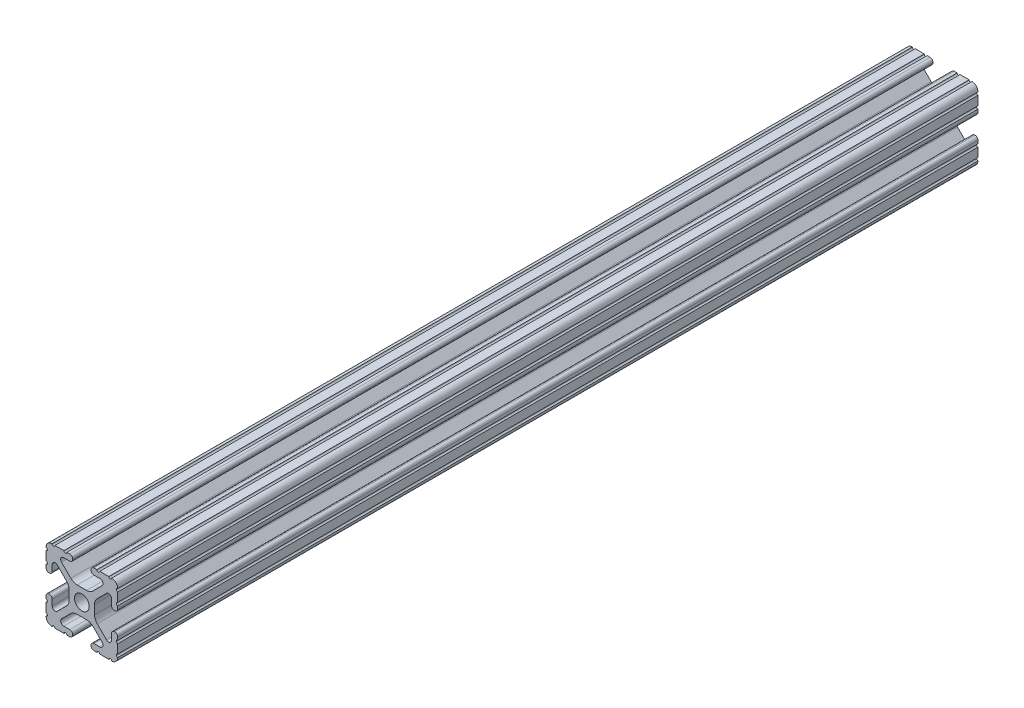
SolidWorks part; units mm, degrees
material "6105-T5 Aluminum"
ref_plane "Front Plane" through (0, 0, 0) normal (0, 0, 1) x (1, 0, 0)
ref_plane "Top Plane" through (0, 0, 0) normal (0, 1, 0) x (1, 0, 0)
ref_plane "Right Plane" through (0, 0, 0) normal (1, 0, 0) x (0, 0, -1)
sketch "Sketch1" plane through (0, 0, 0) normal (0, 0, 1) x (1, 0, 0)
  line L0 (-7.207, 8.7244) -> (-3.8983, 5.4232)
  line L1 (-4.2875, 10.4902) -> (-6.4768, 10.4902)
  line L2 (-3.2385, 11.651) -> (-3.2385, 11.5392)
  line L3 (-5.3171, 12.7) -> (-4.2875, 12.7)
  line L4 (0, 13.4005) -> (0, -14.8534) construction
  line L5 (12.7, 0) -> (-13.9989, 0) construction
  line L6 (-9.5504, 12.7) -> (-6.3331, 12.7)
  line L7 (-12.7, 6.3331) -> (-12.7, 9.5504)
  line L8 (-12.7, 4.2875) -> (-12.7, 5.3171)
  line L9 (-11.5392, 3.2385) -> (-11.651, 3.2385)
  line L10 (-10.4902, 6.4021) -> (-10.4902, 4.2875)
  line L11 (-5.441, 3.8408) -> (-8.7371, 7.1294)
  line L12 (-4.5085, -1.5932) -> (-4.5085, 1.5932)
  line L13 (-1.7093, -4.4958) -> (1.7093, -4.4958)
  line L14 (3.9523, -5.4237) -> (7.1797, -8.6452)
  line L15 (6.4164, -10.4902) -> (4.2875, -10.4902)
  line L16 (3.2385, -11.5392) -> (3.2385, -11.651)
  line L17 (4.2875, -12.7) -> (5.3171, -12.7)
  line L18 (6.3331, -12.7) -> (9.5504, -12.7)
  line L19 (12.7, -9.5504) -> (12.7, -6.3331)
  line L20 (12.7, -5.3171) -> (12.7, -4.2875)
  line L21 (11.651, -3.2385) -> (11.5392, -3.2385)
  line L22 (10.4902, -4.2875) -> (10.4902, -6.4021)
  line L23 (8.7371, -7.1294) -> (5.441, -3.8408)
  line L24 (4.5085, -1.5932) -> (4.5085, 1.5932)
  line L25 (5.441, 3.8408) -> (8.7371, 7.1294)
  line L26 (10.4902, 6.4021) -> (10.4902, 4.2875)
  line L27 (11.5392, 3.2385) -> (11.651, 3.2385)
  line L28 (12.7, 4.2875) -> (12.7, 5.3171)
  line L29 (12.7, 6.3331) -> (12.7, 9.5504)
  line L30 (9.5504, 12.7) -> (6.3331, 12.7)
  line L31 (5.3171, 12.7) -> (4.2875, 12.7)
  line L32 (3.2385, 11.651) -> (3.2385, 11.5392)
  line L33 (4.2875, 10.4902) -> (6.4768, 10.4902)
  line L34 (7.207, 8.7244) -> (3.8983, 5.4232)
  line L35 (1.6558, 4.4958) -> (-1.6558, 4.4958)
  line L36 (-8.7371, -7.1294) -> (-5.441, -3.8408)
  line L37 (-10.4902, -4.2875) -> (-10.4902, -6.4021)
  line L38 (-11.651, -3.2385) -> (-11.5392, -3.2385)
  line L39 (-12.7, -5.3171) -> (-12.7, -4.2875)
  line L40 (-12.7, -9.5504) -> (-12.7, -6.3331)
  line L41 (-6.3331, -12.7) -> (-9.5504, -12.7)
  line L42 (-4.2875, -12.7) -> (-5.3171, -12.7)
  line L43 (-3.2385, -11.5392) -> (-3.2385, -11.651)
  line L44 (-6.4164, -10.4902) -> (-4.2875, -10.4902)
  line L45 (-3.9523, -5.4237) -> (-7.1797, -8.6452)
  arc A0 (-7.207, 8.7244) -> (-6.4768, 10.4902) centre (-6.4768, 9.4563) cw
  arc A1 (-3.2385, 11.5392) -> (-4.2875, 10.4902) centre (-4.2875, 11.5392) cw
  arc A2 (-4.2875, 12.7) -> (-3.2385, 11.651) centre (-4.2875, 11.651) cw
  arc A3 (-5.3171, 12.7) -> (-6.3331, 12.7) centre (-5.8251, 12.7) cw
  arc A4 (-9.5504, 12.7) -> (-10.5664, 12.6998) centre (-10.0584, 12.7) cw
  arc A5 (-12.6998, 10.5664) -> (-10.5664, 12.6998) centre (-10.5918, 10.5918) cw
  arc A6 (-12.6998, 10.5664) -> (-12.7, 9.5504) centre (-12.7, 10.0584) cw
  arc A7 (-12.7, 6.3331) -> (-12.7, 5.3171) centre (-12.7, 5.8251) cw
  arc A8 (-11.651, 3.2385) -> (-12.7, 4.2875) centre (-11.651, 4.2875) cw
  arc A9 (-10.4902, 4.2875) -> (-11.5392, 3.2385) centre (-11.5392, 4.2875) cw
  circle A10 centre (0, 0) radius 2.6035
  arc A11 (-10.4902, 6.4021) -> (-8.7371, 7.1294) centre (-9.4628, 6.4021) cw
  arc A12 (-5.441, 3.8408) -> (-4.5085, 1.5932) centre (-7.6835, 1.5932) cw
  arc A13 (-4.5085, -1.5932) -> (-5.441, -3.8408) centre (-7.6835, -1.5932) cw
  arc A14 (-8.7371, -7.1294) -> (-10.4902, -6.4021) centre (-9.4628, -6.4021) cw
  arc A15 (-1.7093, -4.4958) -> (-3.9523, -5.4237) centre (-1.7093, -7.6708) ccw
  arc A16 (3.9523, -5.4237) -> (1.7093, -4.4958) centre (1.7093, -7.6708) ccw
  arc A17 (6.4164, -10.4902) -> (7.1797, -8.6452) centre (6.4164, -9.4098) ccw
  arc A18 (4.2875, -10.4902) -> (3.2385, -11.5392) centre (4.2875, -11.5392) ccw
  arc A19 (3.2385, -11.651) -> (4.2875, -12.7) centre (4.2875, -11.651) ccw
  arc A20 (6.3331, -12.7) -> (5.3171, -12.7) centre (5.8251, -12.7) ccw
  arc A21 (10.5664, -12.6998) -> (9.5504, -12.7) centre (10.0584, -12.7) ccw
  arc A22 (10.5664, -12.6998) -> (12.6998, -10.5664) centre (10.5918, -10.5918) ccw
  arc A23 (12.7, -9.5504) -> (12.6998, -10.5664) centre (12.7, -10.0584) ccw
  arc A24 (12.7, -5.3171) -> (12.7, -6.3331) centre (12.7, -5.8251) ccw
  arc A25 (12.7, -4.2875) -> (11.651, -3.2385) centre (11.651, -4.2875) ccw
  arc A26 (11.5392, -3.2385) -> (10.4902, -4.2875) centre (11.5392, -4.2875) ccw
  arc A27 (8.7371, -7.1294) -> (10.4902, -6.4021) centre (9.4628, -6.4021) ccw
  arc A28 (4.5085, -1.5932) -> (5.441, -3.8408) centre (7.6835, -1.5932) ccw
  arc A29 (5.441, 3.8408) -> (4.5085, 1.5932) centre (7.6835, 1.5932) ccw
  arc A30 (10.4902, 6.4021) -> (8.7371, 7.1294) centre (9.4628, 6.4021) ccw
  arc A31 (10.4902, 4.2875) -> (11.5392, 3.2385) centre (11.5392, 4.2875) ccw
  arc A32 (11.651, 3.2385) -> (12.7, 4.2875) centre (11.651, 4.2875) ccw
  arc A33 (12.7, 6.3331) -> (12.7, 5.3171) centre (12.7, 5.8251) ccw
  arc A34 (12.6998, 10.5664) -> (12.7, 9.5504) centre (12.7, 10.0584) ccw
  arc A35 (12.6998, 10.5664) -> (10.5664, 12.6998) centre (10.5918, 10.5918) ccw
  arc A36 (9.5504, 12.7) -> (10.5664, 12.6998) centre (10.0584, 12.7) ccw
  arc A37 (5.3171, 12.7) -> (6.3331, 12.7) centre (5.8251, 12.7) ccw
  arc A38 (4.2875, 12.7) -> (3.2385, 11.651) centre (4.2875, 11.651) ccw
  arc A39 (3.2385, 11.5392) -> (4.2875, 10.4902) centre (4.2875, 11.5392) ccw
  arc A40 (7.207, 8.7244) -> (6.4768, 10.4902) centre (6.4768, 9.4563) ccw
  arc A41 (1.6558, 4.4958) -> (3.8983, 5.4232) centre (1.6558, 7.6708) ccw
  arc A42 (-1.6558, 4.4958) -> (-3.8983, 5.4232) centre (-1.6558, 7.6708) cw
  arc A43 (-11.5392, -3.2385) -> (-10.4902, -4.2875) centre (-11.5392, -4.2875) cw
  arc A44 (-12.7, -4.2875) -> (-11.651, -3.2385) centre (-11.651, -4.2875) cw
  arc A45 (-12.7, -5.3171) -> (-12.7, -6.3331) centre (-12.7, -5.8251) cw
  arc A46 (-12.7, -9.5504) -> (-12.6998, -10.5664) centre (-12.7, -10.0584) cw
  arc A47 (-10.5664, -12.6998) -> (-12.6998, -10.5664) centre (-10.5918, -10.5918) cw
  arc A48 (-10.5664, -12.6998) -> (-9.5504, -12.7) centre (-10.0584, -12.7) cw
  arc A49 (-6.3331, -12.7) -> (-5.3171, -12.7) centre (-5.8251, -12.7) cw
  arc A50 (-3.2385, -11.651) -> (-4.2875, -12.7) centre (-4.2875, -11.651) cw
  arc A51 (-4.2875, -10.4902) -> (-3.2385, -11.5392) centre (-4.2875, -11.5392) cw
  arc A52 (-6.4164, -10.4902) -> (-7.1797, -8.6452) centre (-6.4164, -9.4098) cw
  dimension "D1" = 5.207
  dimension "D9" = 14.859
  dimension "D2" = 25.4
  dimension "D3" = 12.7
  dimension "D4" = 6.477
  dimension "D5" = 8.2042
  dimension "D6" = 9.017
  dimension "D8" = 2.2098
  dimension "D10" = 2.2098
extrude "Extrude1" add sketch "Sketch1" against normal blind 304.8
